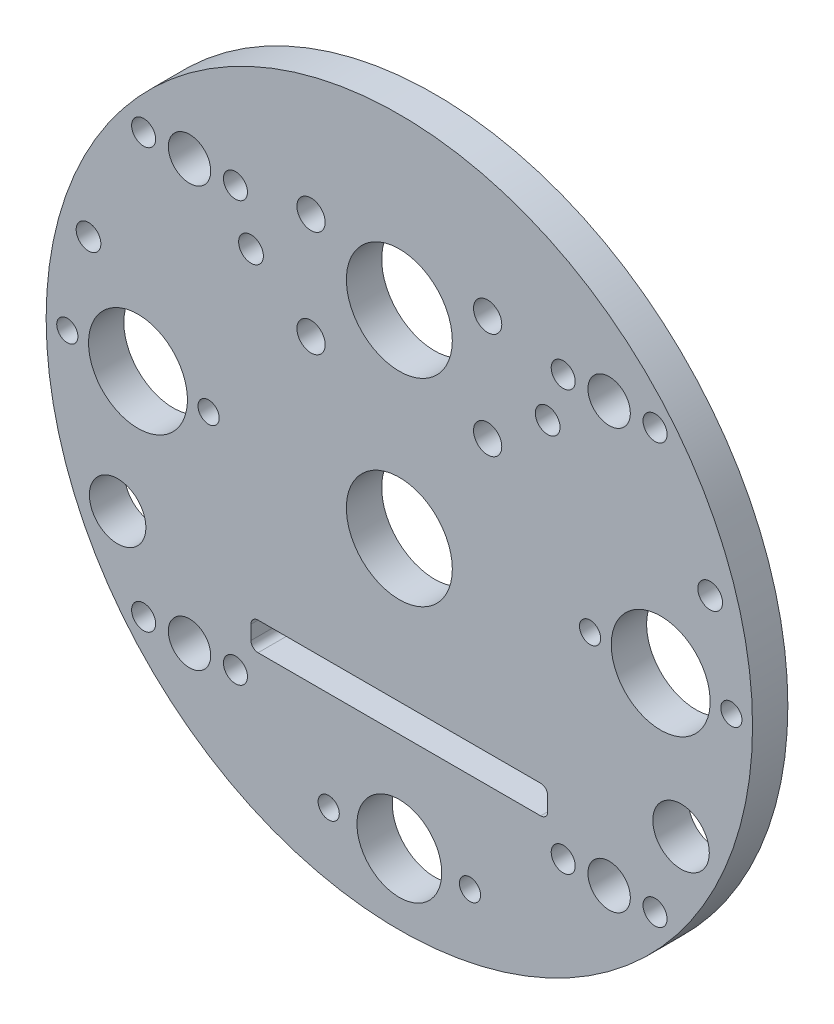
SolidWorks part; units mm, degrees
material "Acrylic (Medium-high impact)"
ref_plane "Front Plane" through (0, 0, 0) normal (0, 0, 1) x (1, 0, 0)
ref_plane "Top Plane" through (0, 0, 0) normal (0, 1, 0) x (1, 0, 0)
ref_plane "Right Plane" through (0, 0, 0) normal (1, 0, 0) x (0, 0, -1)
sketch "Sketch1" plane through (0, 0, 0) normal (0, 0, 1) x (1, 0, 0)
  circle A0 centre (0, 0) radius 50
  dimension "D1" = 100
extrude "Boss-Extrude1" add sketch "Sketch1" along normal blind 5
hole_wizard "Ø14.0 (14) Diameter Hole1" positions "Sketch5" profile "Sketch6" hole size "Ø14.0" standard "ISO"
sketch "Sketch5" plane through (0, 0, 0) normal (0, 0, -1) x (-1, 0, 0)
  point P4 (37, 0)
  point P17 (-37, 0)
  point P21 (0, -37) [skipped]
  dimension "D1" = 3
  dimension "D3" = 37
sketch "Sketch6" plane through (-37, 0, 0) normal (1, 0, 0) x (0, 1, 0)
  line L0 (0, 0) -> (0, 5)
  line L1 (0, 5) -> (7, 5)
  line L2 (7, 5) -> (7, 0)
  line L5 (7, 0) -> (0, 0)
  line L11 (0, -6.35) -> (0, 107.95) construction
  dimension "Thru Hole Dia." = 14
  dimension "Thru Hole Depth" = 5
sketch "Sketch9" plane through (0, 0, 5) normal (0, 0, 1) x (1, 0, 0)
  circle A0 centre (0, 26) radius 7.5
  dimension "D1" = 15
  dimension "D2" = 26
extrude "Cut-Extrude1" cut sketch "Sketch9" against normal blind 10
sketch "Sketch10" plane through (0, 0, 5) normal (0, 0, 1) x (1, 0, 0)
  line L0 (0, 0) -> (0, 43.8595) construction
  circle A0 centre (-12.5, 31.5) radius 2
  circle A1 centre (0, 26) radius 7.5 construction
  circle A2 centre (-12.5, 16.5) radius 2
  circle A3 centre (12.5, 31.5) radius 2
  circle A4 centre (12.5, 16.5) radius 2
  dimension "D1" = 4
  dimension "D2" = 12.5
  dimension "D3" = 5.5
  dimension "D4" = 4
  dimension "D5" = 9.5
extrude "Cut-Extrude2" cut sketch "Sketch10" against normal blind 10
sketch "Sketch11" plane through (0, 0, 5) normal (0, 0, 1) x (1, 0, 0)
  circle A0 centre (0, -2) radius 7.5
  dimension "D1" = 15
  dimension "D2" = 2
extrude "Cut-Extrude3" cut sketch "Sketch11" against normal blind 10
sketch "Sketch12" plane through (0, 0, 5) normal (0, 0, 1) x (1, 0, 0)
  line L0 (0, 0) -> (0, 7.8465) construction
  line L1 (0, 0) -> (-29.6985, 29.6985) construction
  circle A0 centre (-29.6985, 29.6985) radius 3
  dimension "D3" = 6
  dimension "D1" = 45
  dimension "D2" = 42
extrude "Cut-Extrude4" cut sketch "Sketch12" against normal blind 10
pattern_circular "CirPattern1" count 4 over 360 about axis through (0, 0, 0) along (0, 0, 1) of "Cut-Extrude4"
sketch "Sketch13" plane through (0, 0, 5) normal (0, 0, 1) x (1, 0, 0)
  circle A0 centre (-47, 0) radius 1.5
  circle A1 centre (-27, 0) radius 1.5
  circle A2 centre (27, 0) radius 1.5
  circle A3 centre (47, 0) radius 1.5
  circle A4 centre (10, -40) radius 1.5
  circle A5 centre (-10, -40) radius 1.5
  circle A6 centre (-37, 0) radius 7 construction
  circle A7 centre (37, 0) radius 7 construction
  circle A8 centre (0, -40) radius 6
  dimension "D1" = 3
  dimension "D2" = 3
  dimension "D3" = 3
  dimension "D4" = 3
  dimension "D5" = 3
  dimension "D6" = 3
  dimension "D7" = 10
  dimension "D8" = 10
  dimension "D9" = 10
  dimension "D10" = 10
  dimension "D11" = 40
  dimension "D12" = 10
  dimension "D15" = 12
  dimension "D16" = 10
  dimension "D13" = 40
  dimension "D14" = 40
extrude "Cut-Extrude5" cut sketch "Sketch13" against normal blind 10
sketch "Sketch14" plane through (0, 0, 5) normal (0, 0, 1) x (1, 0, 0)
  circle A0 centre (-21, 23) radius 1.75
  circle A1 centre (-44, 13) radius 1.75
  dimension "D1" = 3.5
  dimension "D2" = 3.5
  dimension "D3" = 10
  dimension "D4" = 23
  dimension "D5" = 44
  dimension "D6" = 13
extrude "Cut-Extrude6" cut sketch "Sketch14" against normal blind 10
mirror "Mirror1" about plane through (0, 0, 0) normal (1, 0, 0) of "Cut-Extrude6"
sketch "Sketch15" plane through (0, 0, 5) normal (0, 0, 1) x (1, 0, 0)
  line L0 (0, 0) -> (-39.8775, -18.5952) construction
  line L1 (0, 0) -> (0, -16.4933) construction
  circle A0 centre (-39.8775, -18.5952) radius 4
  circle A1 centre (39.8775, -18.5952) radius 4
  dimension "D1" = 8
  dimension "D2" = 44
  dimension "D3" = 65
extrude "Cut-Extrude7" cut sketch "Sketch15" against normal blind 10
sketch "Sketch16" plane through (0, 0, 5) normal (0, 0, 1) x (1, 0, 0)
  line L0 (-20, -22) -> (20, -22)
  line L1 (-21, -23) -> (-21, -25)
  line L2 (-20, -26) -> (20, -26)
  line L3 (21, -23) -> (21, -25)
  arc A0 (-20, -22) -> (-21, -23) centre (-20, -23) ccw
  arc A1 (-21, -25) -> (-20, -26) centre (-20, -25) ccw
  arc A2 (21, -25) -> (20, -26) centre (20, -25) cw
  arc A3 (21, -23) -> (20, -22) centre (20, -23) ccw
  point P6 (-21, -22)
  point P10 (-21, -26)
  point P13 (21, -26)
  dimension "D3" = 1
  dimension "D1" = 4
  dimension "D2" = 42
  dimension "D9" = 26
  dimension "D10" = 21
extrude "Cut-Extrude8" cut sketch "Sketch16" against normal blind 10
hole_wizard "M3 Clearance Hole1" positions "Sketch17" profile "Sketch19" hole size "M3" standard "ISO" end condition through all
sketch "Sketch17" plane through (0, 0, 5) normal (0, 0, 1) x (1, 0, 0)
  circle A1 centre (-29.6985, -29.6985) radius 3 construction
  point P0 (-36.1985, -29.6985)
  point P2 (-23.1985, -29.6985)
  dimension "D1" = 6
  dimension "D2" = 13
  dimension "D3" = 6.5
sketch "Sketch19" plane through (-36.1985, -29.6985, 5) normal (1, 0, 0) x (0, -1, 0)
  line L0 (0, 0) -> (0, 5)
  line L1 (0, 5) -> (1.7, 5)
  line L2 (1.7, 5) -> (1.7, 0)
  line L5 (1.7, 0) -> (0, 0)
  line L11 (0, -6.35) -> (0, 107.95) construction
  dimension "Thru Hole Dia." = 3.4
  dimension "Thru Hole Depth" = 5
mirror "Mirror2" about plane through (0, 0, 0) normal (0, 1, 0) of "M3 Clearance Hole1"
mirror "Mirror3" about plane through (0, 0, 0) normal (1, 0, 0) of "Mirror2", "M3 Clearance Hole1"
